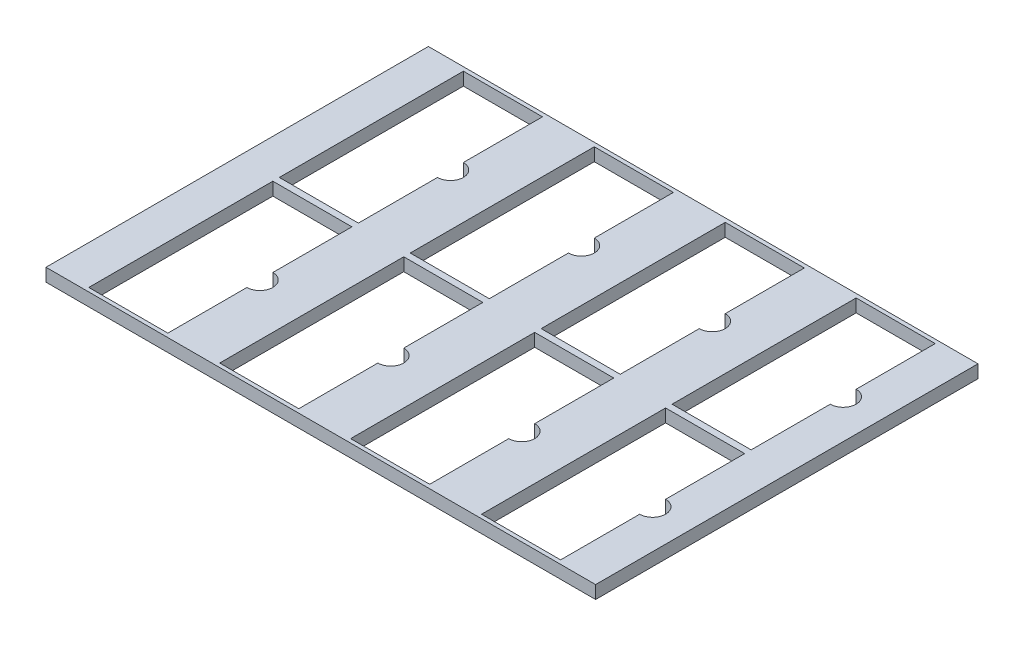
SolidWorks part; units mm, degrees
ref_plane "Front Plane" through (0, 0, 0) normal (0, 0, 1) x (1, 0, 0)
ref_plane "Top Plane" through (0, 0, 0) normal (0, 1, 0) x (1, 0, 0)
ref_plane "Right Plane" through (0, 0, 0) normal (1, 0, 0) x (0, 0, -1)
sketch "Sketch1" plane through (0, 0, 0) normal (0, 1, 0) x (1, 0, 0)
  line L1 (-212, 147.5) -> (212, 147.5)
  line L2 (-212, 147.5) -> (-212, -147.5)
  line L3 (-212, -147.5) -> (212, -147.5)
  line L4 (212, 147.5) -> (212, -147.5)
  line L5 (-212, 147.5) -> (212, -147.5) construction
  line L6 (-212, -147.5) -> (212, 147.5) construction
  line L7 (-182, 144.5) -> (-121, 144.5)
  line L8 (-182, 144.5) -> (-182, 2.5)
  line L9 (-182, 2.5) -> (-121, 2.5)
  line L10 (-121, 144.5) -> (-121, 83.5)
  line L42 (-121, 73.5) -> (182, 73.5) construction
  line L44 (-121, 63.5) -> (-121, 2.5)
  line L45 (-20, 63.5) -> (-20, 2.5)
  line L46 (-81, 2.5) -> (-20, 2.5)
  line L47 (-81, 144.5) -> (-81, 2.5)
  line L48 (-81, 144.5) -> (-20, 144.5)
  line L49 (-20, 144.5) -> (-20, 83.5)
  line L50 (81, 63.5) -> (81, 2.5)
  line L51 (20, 2.5) -> (81, 2.5)
  line L52 (20, 144.5) -> (20, 2.5)
  line L53 (20, 144.5) -> (81, 144.5)
  line L54 (81, 144.5) -> (81, 83.5)
  line L55 (182, 63.5) -> (182, 2.5)
  line L56 (121, 2.5) -> (182, 2.5)
  line L57 (121, 144.5) -> (121, 2.5)
  line L58 (121, 144.5) -> (182, 144.5)
  line L59 (182, 144.5) -> (182, 83.5)
  line L60 (-20, -63.5) -> (-20, -2.5)
  line L61 (-121, -144.5) -> (-121, -83.5)
  line L62 (-182, -144.5) -> (-121, -144.5)
  line L63 (-182, -144.5) -> (-182, -2.5)
  line L64 (-182, -2.5) -> (-121, -2.5)
  line L65 (-121, -63.5) -> (-121, -2.5)
  line L66 (-81, -2.5) -> (-20, -2.5)
  line L67 (-81, -144.5) -> (-81, -2.5)
  line L68 (-81, -144.5) -> (-20, -144.5)
  line L69 (-20, -144.5) -> (-20, -83.5)
  line L70 (81, -63.5) -> (81, -2.5)
  line L71 (20, -2.5) -> (81, -2.5)
  line L72 (20, -144.5) -> (20, -2.5)
  line L73 (20, -144.5) -> (81, -144.5)
  line L74 (81, -144.5) -> (81, -83.5)
  line L75 (182, -63.5) -> (182, -2.5)
  line L76 (121, -2.5) -> (182, -2.5)
  line L77 (121, -144.5) -> (121, -2.5)
  line L78 (121, -144.5) -> (182, -144.5)
  line L79 (182, -144.5) -> (182, -83.5)
  arc A0 (-121, 83.5) -> (-121, 63.5) centre (-121, 73.5) cw
  arc A1 (-20, 83.5) -> (-20, 63.5) centre (-20, 73.5) cw
  arc A2 (81, 83.5) -> (81, 63.5) centre (81, 73.5) cw
  arc A3 (182, 83.5) -> (182, 63.5) centre (182, 73.5) cw
  arc A4 (-121, -83.5) -> (-121, -63.5) centre (-121, -73.5) ccw
  arc A5 (-20, -83.5) -> (-20, -63.5) centre (-20, -73.5) ccw
  arc A6 (81, -83.5) -> (81, -63.5) centre (81, -73.5) ccw
  arc A7 (182, -83.5) -> (182, -63.5) centre (182, -73.5) ccw
  point P0 (0, 0)
  dimension "D15" = 10
  dimension "D8" = 71
  dimension "D12" = 10
  dimension "D13" = 71
  dimension "D1" = 424
  dimension "D2" = 295
  dimension "D3" = 142
  dimension "D4" = 3
  dimension "D5" = 61
  dimension "D6" = 30
  dimension "D9" = 3
  dimension "D10" = 30
  dimension "D11" = 5
  dimension "D14" = 4
  dimension "D16" = 40
  dimension "D7" = 4
extrude "Boss-Extrude1" add sketch "Sketch1" along normal blind 10
